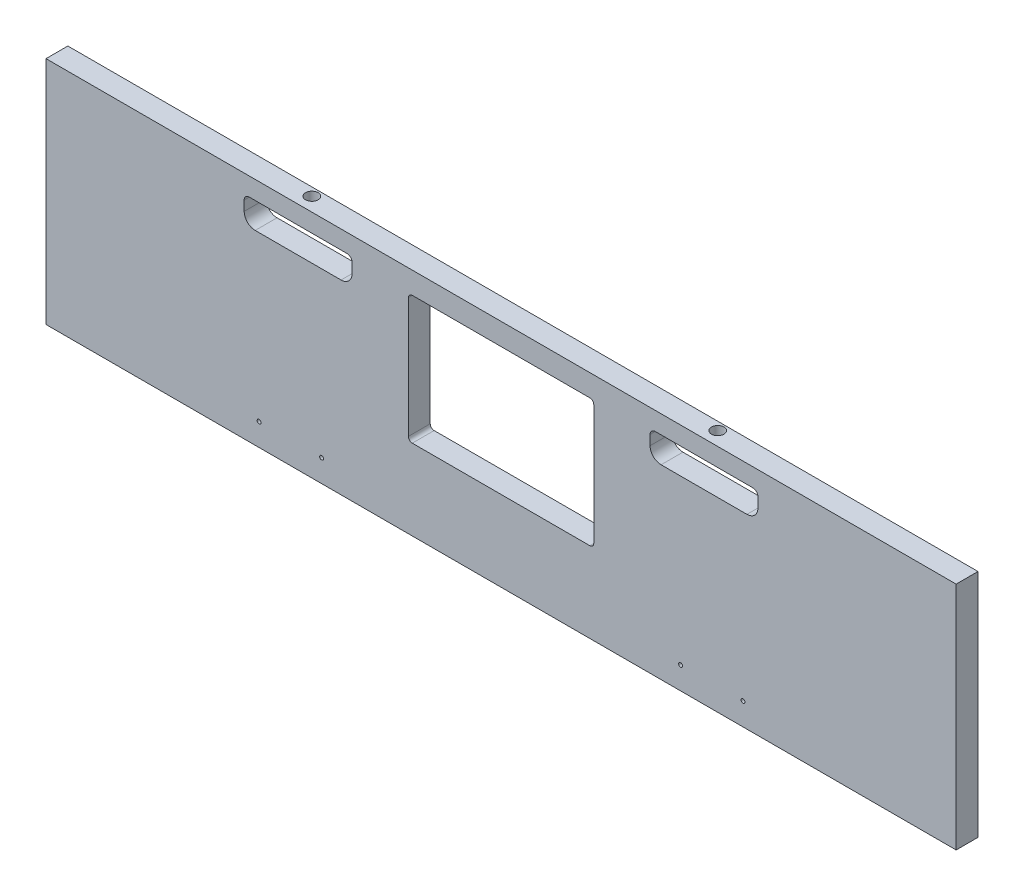
SolidWorks part; units mm, degrees
material "Cedar"
ref_plane "Front Plane" through (0, 0, 0) normal (0, 0, 1) x (1, 0, 0)
ref_plane "Top Plane" through (0, 0, 0) normal (0, 1, 0) x (1, 0, 0)
ref_plane "Right Plane" through (0, 0, 0) normal (1, 0, 0) x (0, 0, -1)
sketch "Sketch1" plane through (0, 0, 0) normal (0, 0, 1) x (1, 0, 0)
  line L0 (-163.9887, -5335.905) -> (-163.9887, -5432.425)
  line L1 (-102.87, -5350.891) -> (-33.02, -5350.891)
  line L2 (-111.8235, -5341.9375) -> (-111.8235, -5334)
  line L3 (-24.0665, -5341.9375) -> (-24.0665, -5334)
  line L4 (-298.9262, -5332.73) -> (-167.1637, -5332.73)
  line L5 (-167.1637, -5435.6) -> (-298.9262, -5435.6)
  line L6 (-302.1012, -5432.425) -> (-302.1012, -5335.905)
  line L7 (-107.6325, -5329.809) -> (-28.2575, -5329.809)
  line L8 (174.9425, -5308.6) -> (174.9425, -5581.65)
  line L9 (449.2625, -5413.1661) -> (449.2625, -5421.9659)
  line L10 (595.3125, -5421.9659) -> (595.3125, -5413.1661)
  line L11 (839.47, -5509.5521) -> (839.47, -5307.6729)
  line L12 (839.47, -5307.6729) -> (863.6, -5307.6729)
  line L13 (839.47, -5509.5521) -> (863.6, -5509.5521)
  line L14 (863.6, -5509.5521) -> (863.6, -5307.6729)
  line L15 (-354.2665, -5341.9375) -> (-354.2665, -5334)
  line L16 (-100.8856, -5889.625) -> (-50.0856, -5889.625)
  line L17 (-104.0606, -5969) -> (-104.0606, -5892.8)
  line L18 (-46.9106, -5892.8) -> (-46.9106, -5969)
  line L19 (-50.0856, -5972.175) -> (-100.8856, -5972.175)
  line L20 (-100.8856, -5848.35) -> (-50.0856, -5848.35)
  line L21 (857.25, -5502.275) -> (157.1625, -5575.3)
  line L22 (857.25, -5314.95) -> (857.25, -5502.275)
  line L23 (157.1625, -5314.95) -> (157.1625, -5575.3)
  line L24 (857.25, -5314.95) -> (157.1625, -5314.95)
  line L25 (150.8125, -5308.6) -> (174.9425, -5308.6)
  line L26 (174.9425, -5581.65) -> (150.8125, -5581.65)
  line L27 (137.16, -5314.95) -> (137.16, -5502.275)
  line L28 (150.8125, -5581.65) -> (150.8125, -5308.6)
  line L29 (590.8224, -5408.676) -> (453.7526, -5408.676)
  line L30 (453.7526, -5426.456) -> (590.8224, -5426.456)
  line L31 (137.16, -6013.45) -> (137.16, -5867.4)
  line L32 (150.8125, -5746.75) -> (150.8125, -6019.8)
  line L33 (143.51, -5639.9938) -> (143.51, -5654.294)
  line L34 (590.8224, -5919.724) -> (453.7526, -5919.724)
  line L35 (453.7526, -5901.944) -> (590.8224, -5901.944)
  line L36 (449.2625, -5915.2339) -> (449.2625, -5906.4341)
  line L37 (174.9425, -6019.8) -> (174.9425, -5746.75)
  line L38 (595.3125, -5906.4341) -> (595.3125, -5915.2339)
  line L39 (839.47, -5818.8479) -> (839.47, -6020.7271)
  line L40 (839.47, -5818.8479) -> (863.6, -5818.8479)
  line L41 (863.6, -5818.8479) -> (863.6, -6020.7271)
  line L42 (839.47, -6020.7271) -> (863.6, -6020.7271)
  line L43 (-155.8782, -5867.4) -> (-603.25, -5867.4)
  line L44 (-433.07, -5350.891) -> (-363.22, -5350.891)
  line L45 (-437.8325, -5329.809) -> (-358.4575, -5329.809)
  line L46 (889, -6045.2) -> (-635, -6045.2)
  line L47 (-635, -5283.2) -> (889, -5283.2)
  line L48 (-635, -6045.2) -> (-635, -5283.2)
  line L49 (889, -5283.2) -> (889, -6045.2)
  line L50 (137.16, -5502.275) -> (-603.25, -5502.275)
  line L51 (-603.25, -5314.95) -> (137.16, -5314.95)
  line L52 (143.51, -5654.294) -> (-609.6, -5654.294)
  line L53 (-609.6, -5639.9938) -> (143.51, -5639.9938)
  line L54 (137.16, -5536.0062) -> (-603.25, -5536.0062)
  line L55 (-603.25, -5794.375) -> (137.16, -5794.375)
  line L56 (-603.25, -6013.45) -> (137.16, -6013.45)
  line L57 (-603.25, -5536.0062) -> (-603.25, -5794.375)
  line L58 (137.16, -5794.375) -> (137.16, -5536.0062)
  line L59 (-609.6, -5654.294) -> (-609.6, -5639.9938)
  line L60 (-603.25, -5867.4) -> (-603.25, -6013.45)
  line L61 (-603.25, -5314.95) -> (-603.25, -5502.275)
  line L62 (-442.0235, -5341.9375) -> (-442.0235, -5334)
  line L63 (857.25, -5826.125) -> (157.1625, -5753.1)
  line L64 (857.25, -6013.45) -> (857.25, -5826.125)
  line L65 (157.1625, -6013.45) -> (157.1625, -5753.1)
  line L66 (857.25, -6013.45) -> (157.1625, -6013.45)
  line L67 (174.9425, -5746.75) -> (150.8125, -5746.75)
  line L68 (150.8125, -6019.8) -> (174.9425, -6019.8)
  line L69 (137.16, -5867.4) -> (4.907, -5867.4)
  circle A0 centre (-36.195, -5484.0124) radius 1.5875
  arc A1 (-298.9262, -5332.73) -> (-302.1012, -5335.905) centre (-298.9262, -5335.905) ccw
  arc A2 (-302.1012, -5432.425) -> (-298.9262, -5435.6) centre (-298.9262, -5432.425) ccw
  arc A3 (-163.9887, -5335.905) -> (-167.1637, -5332.73) centre (-167.1637, -5335.905) ccw
  arc A4 (-167.1637, -5435.6) -> (-163.9887, -5432.425) centre (-167.1637, -5432.425) ccw
  arc A5 (-111.8235, -5341.9375) -> (-102.87, -5350.891) centre (-102.87, -5341.9375) ccw
  arc A6 (-107.6325, -5329.809) -> (-111.8235, -5334) centre (-107.6325, -5334) ccw
  circle A7 centre (166.0525, -5444.6613) radius 1.5875
  circle A8 centre (166.0525, -5358.1871) radius 1.5875
  circle A9 centre (471.4875, -5417.566) radius 1.5875
  arc A10 (453.7526, -5408.676) -> (449.2625, -5413.1661) centre (451.5076, -5410.9211) ccw
  arc A11 (449.2625, -5421.9659) -> (453.7526, -5426.456) centre (451.5076, -5424.2109) ccw
  circle A12 centre (522.2875, -5417.566) radius 1.5875
  circle A13 centre (573.0875, -5417.566) radius 1.5875
  arc A14 (590.8224, -5426.456) -> (595.3125, -5421.9659) centre (593.0674, -5424.2109) ccw
  arc A15 (595.3125, -5413.1661) -> (590.8224, -5408.676) centre (593.0674, -5410.9211) ccw
  circle A16 centre (848.36, -5471.8269) radius 1.5875
  circle A17 centre (848.36, -5409.0762) radius 1.5875
  circle A18 centre (848.36, -5346.3254) radius 1.5875
  arc A19 (-363.22, -5350.891) -> (-354.2665, -5341.9375) centre (-363.22, -5341.9375) ccw
  arc A20 (-354.2665, -5334) -> (-358.4575, -5329.809) centre (-358.4575, -5334) ccw
  arc A21 (-24.0665, -5334) -> (-28.2575, -5329.809) centre (-28.2575, -5334) ccw
  arc A22 (-33.02, -5350.891) -> (-24.0665, -5341.9375) centre (-33.02, -5341.9375) ccw
  circle A23 centre (-86.995, -5484.0124) radius 1.5875
  circle A24 centre (-333.4544, -5894.07) radius 2.54
  circle A25 centre (-333.4544, -5994.4) radius 2.54
  arc A26 (-104.0606, -5969) -> (-100.8856, -5972.175) centre (-100.8856, -5969) ccw
  arc A27 (-50.0856, -5972.175) -> (-46.9106, -5969) centre (-50.0856, -5969) ccw
  arc A28 (-100.8856, -5848.35) -> (-128.3819, -5857.875) centre (-100.8856, -5892.8) ccw
  arc A29 (-155.8782, -5867.4) -> (-128.3819, -5857.875) centre (-155.8782, -5822.95) ccw
  arc A30 (-22.5893, -5857.875) -> (-50.0856, -5848.35) centre (-50.0856, -5892.8) ccw
  circle A31 centre (-132.6356, -5894.07) radius 2.54
  circle A32 centre (-132.6356, -5994.4) radius 2.54
  arc A33 (-46.9106, -5892.8) -> (-50.0856, -5889.625) centre (-50.0856, -5892.8) ccw
  arc A34 (-100.8856, -5889.625) -> (-104.0606, -5892.8) centre (-100.8856, -5892.8) ccw
  arc A35 (-22.5893, -5857.875) -> (4.907, -5867.4) centre (4.907, -5822.95) ccw
  circle A36 centre (166.0525, -5531.1356) radius 1.5875
  arc A37 (449.2625, -5915.2339) -> (453.7526, -5919.724) centre (451.5076, -5917.4789) ccw
  arc A38 (453.7526, -5901.944) -> (449.2625, -5906.4341) centre (451.5076, -5904.1891) ccw
  circle A39 centre (166.0525, -5797.2644) radius 1.5875
  circle A40 centre (166.0525, -5883.7387) radius 1.5875
  circle A41 centre (166.0525, -5970.2129) radius 1.5875
  circle A42 centre (471.4875, -5910.834) radius 1.5875
  circle A43 centre (522.2875, -5910.834) radius 1.5875
  circle A44 centre (573.0875, -5910.834) radius 1.5875
  arc A45 (595.3125, -5906.4341) -> (590.8224, -5901.944) centre (593.0674, -5904.1891) ccw
  arc A46 (590.8224, -5919.724) -> (595.3125, -5915.2339) centre (593.0674, -5917.4789) ccw
  circle A47 centre (848.36, -5919.3238) radius 1.5875
  circle A48 centre (848.36, -5982.0746) radius 1.5875
  circle A49 centre (848.36, -5856.5731) radius 1.5875
  arc A50 (-437.8325, -5329.809) -> (-442.0235, -5334) centre (-437.8325, -5334) ccw
  circle A51 centre (-429.895, -5484.0124) radius 1.5875
  arc A52 (-442.0235, -5341.9375) -> (-433.07, -5350.891) centre (-433.07, -5341.9375) ccw
  circle A53 centre (-379.095, -5484.0124) radius 1.5875
sketch "HeadBottomOutline" plane through (0, 0, 0) normal (0, 0, 1) x (1, 0, 0)
  line L0 (137.16, -5502.275) -> (137.16, -5314.95)
  line L1 (137.16, -5314.95) -> (-603.25, -5314.95)
  line L2 (-603.25, -5314.95) -> (-603.25, -5502.275)
  line L3 (-603.25, -5502.275) -> (137.16, -5502.275)
  line L4 (-233.045, -5502.275) -> (-233.045, -5314.95) construction
  line L5 (-603.25, -5408.6125) -> (-233.045, -5408.6125) construction
  line L6 (137.16, -5408.6125) -> (-233.045, -5408.6125) construction
  dimension "Length" = 740.41
  dimension "Width" = 187.325
extrude "HeadBottomOutline_Thickness" add sketch "HeadBottomOutline" against normal blind 17.78
sketch "Sketch3" plane through (0, 0, 0) normal (0, 0, 1) x (1, 0, 0)
  line L0 (-308.4512, -5335.905) -> (-308.4512, -5433.695)
  line L1 (-305.2762, -5436.87) -> (-160.8137, -5436.87)
  line L2 (-157.6387, -5433.695) -> (-157.6387, -5335.905)
  line L3 (-160.8137, -5332.73) -> (-305.2762, -5332.73)
  line L4 (-354.2665, -5334) -> (-354.2665, -5341.9375)
  line L5 (-363.22, -5350.891) -> (-433.07, -5350.891)
  line L6 (-442.0235, -5341.9375) -> (-442.0235, -5334)
  line L7 (-437.8325, -5329.809) -> (-358.4575, -5329.809)
  line L8 (-102.87, -5350.891) -> (-33.02, -5350.891)
  line L9 (-24.0665, -5341.9375) -> (-24.0665, -5334)
  line L10 (-28.2575, -5329.809) -> (-107.6325, -5329.809)
  line L11 (-111.8235, -5334) -> (-111.8235, -5341.9375)
  line L12 (-148.1137, -5332.73) -> (-317.9762, -5332.73) construction
  line L16 (-157.6387, -5461.3175) -> (-157.6387, -5332.73) construction
  line L17 (-308.4512, -5332.73) -> (-308.4512, -5461.3175) construction
  line L21 (-420.37, -5436.87) -> (-45.72, -5436.87) construction
  line L22 (-398.145, -5329.809) -> (-398.145, -5314.95) construction
  line L23 (137.16, -5314.95) -> (-603.25, -5314.95) construction
  line L24 (-398.145, -5329.809) -> (-398.145, -5350.891) construction
  arc A0 (-308.4512, -5433.695) -> (-305.2762, -5436.87) centre (-305.2762, -5433.695) ccw
  arc A1 (-160.8137, -5436.87) -> (-157.6387, -5433.695) centre (-160.8137, -5433.695) ccw
  arc A2 (-157.6387, -5335.905) -> (-160.8137, -5332.73) centre (-160.8137, -5335.905) ccw
  arc A3 (-305.2762, -5332.73) -> (-308.4512, -5335.905) centre (-305.2762, -5335.905) ccw
  arc A4 (-354.2665, -5341.9375) -> (-363.22, -5350.891) centre (-363.22, -5341.9375) cw
  arc A5 (-433.07, -5350.891) -> (-442.0235, -5341.9375) centre (-433.07, -5341.9375) cw
  arc A6 (-442.0235, -5334) -> (-437.8325, -5329.809) centre (-437.8325, -5334) cw
  arc A7 (-358.4575, -5329.809) -> (-354.2665, -5334) centre (-358.4575, -5334) cw
  arc A8 (-33.02, -5350.891) -> (-24.0665, -5341.9375) centre (-33.02, -5341.9375) ccw
  arc A9 (-24.0665, -5334) -> (-28.2575, -5329.809) centre (-28.2575, -5334) ccw
  arc A10 (-107.6325, -5329.809) -> (-111.8235, -5334) centre (-107.6325, -5334) ccw
  arc A11 (-111.8235, -5341.9375) -> (-102.87, -5350.891) centre (-102.87, -5341.9375) ccw
  circle A12 centre (-429.895, -5484.0124) radius 1.5875
  circle A13 centre (-379.095, -5484.0124) radius 1.5875
  circle A14 centre (-86.995, -5484.0124) radius 1.5875
  circle A15 centre (-36.195, -5484.0124) radius 1.5875
  point P16 (-509.5773, -5301.4203)
  dimension "D1" = 21.082
  dimension "D2" = 14.859
extrude "Cut-Extrude1" cut sketch "Sketch3" against normal up to surface (17.78 mm away) up to face at (-233.045, -5408.6125, -17.78)
sketch "Sketch4" plane through (0, -5314.95, 0) normal (0, 1, 0) x (1, 0, 0)
  circle A0 centre (-67.97, 11.1873) radius 5.08
  circle A1 centre (-398.17, 11.1873) radius 5.08
extrude "Cut-Extrude2" cut sketch "Sketch4" against normal up to surface (14.859 mm away) up to face at (-67.945, -5329.809, -8.89)
